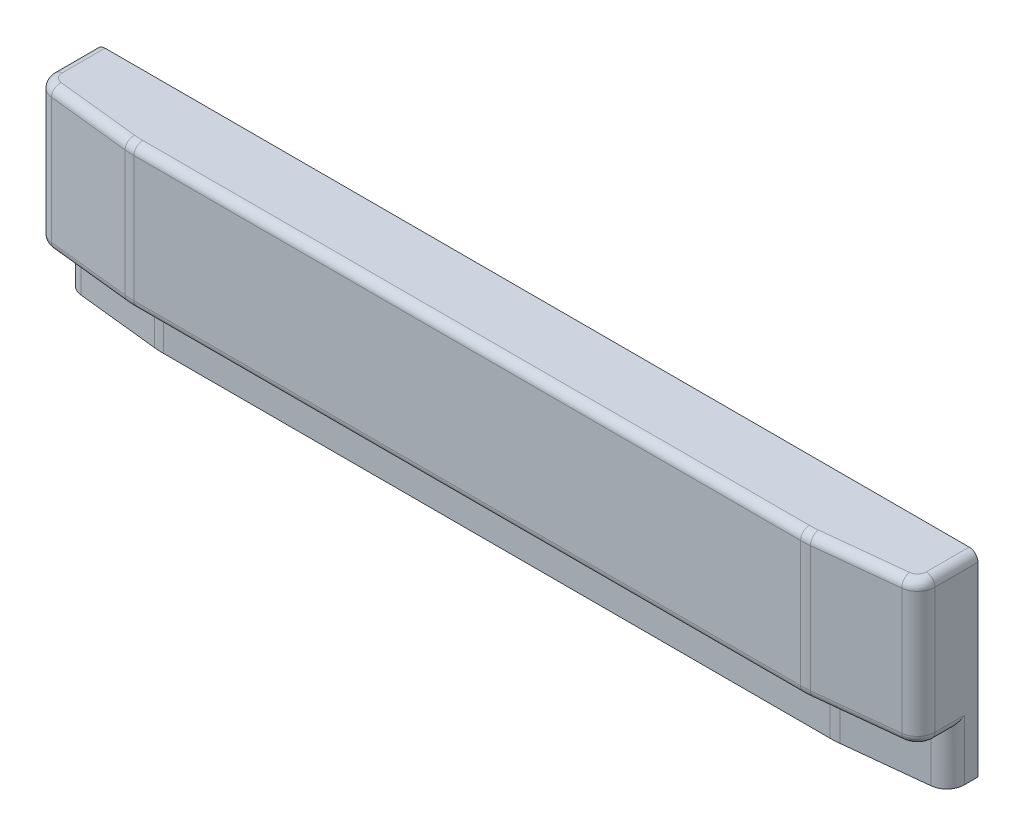
SolidWorks part; units mm, degrees
other "Camera1"
ref_plane "Front Plane" through (0, 0, 0) normal (0, 0, 1) x (1, 0, 0)
ref_plane "Top Plane" through (0, 0, 0) normal (0, 1, 0) x (1, 0, 0)
ref_plane "Right Plane" through (0, 0, 0) normal (1, 0, 0) x (0, 0, -1)
sketch "Sketch7" plane through (0, 0, 0) normal (0, 1, 0) x (1, 0, 0)
  line L0 (0, 0) -> (762, 0)
  line L1 (762, 0) -> (762, -50.8)
  line L2 (762, -50.8) -> (673.1, -60.325)
  line L3 (673.1, -60.325) -> (88.9, -60.325)
  line L4 (88.9, -60.325) -> (0, -50.8)
  line L5 (0, -50.8) -> (0, 0)
  dimension "D1" = 762
  dimension "D2" = 50.8
  dimension "D3" = 88.9
  dimension "D4" = 88.9
  dimension "D5" = 60.325
extrude "Boss-Extrude1" add sketch "Sketch7" along normal blind 168.275
ref_plane "Wall Plane" through (0, 0, 0) normal (0, 0, 1) x (1, 0, 0)
ref_plane "Floor Plane" through (0, 0, 0) normal (0, 1, 0) x (1, 0, 0)
sketch "Sketch10" plane through (0, 0, 0) normal (0, -1, 0) x (1, 0, 0)
  line L0 (0, 50.8) -> (0, 25.4)
  line L1 (0, 0) -> (0, 50.8) construction
  line L2 (0, 25.4) -> (88.9, 34.925)
  line L3 (88.9, 34.925) -> (673.1, 34.925)
  line L4 (673.1, 34.925) -> (762, 25.4)
  line L5 (762, 50.8) -> (762, 0) construction
  line L6 (762, 25.4) -> (762, 50.8)
  line L7 (762, 50.8) -> (673.1, 60.325)
  line L8 (673.1, 60.325) -> (88.9, 60.325)
  line L9 (88.9, 60.325) -> (0, 50.8)
  dimension "D1" = 25.4
extrude "Cut-Extrude1" cut sketch "Sketch10" against normal blind 44.45
fillet "Fillet1" radius 15.24 4 edges at (762, 22.225, 25.4) (762, 106.3625, 50.8) (0, 22.225, 25.4) (0, 106.3625, 50.8)
fillet "Fillet2" radius 76.2 4 edges at (673.1, 22.225, 34.925) (673.1, 106.3625, 60.325) (88.9, 22.225, 34.925) (88.9, 106.3625, 60.325)
fillet "Fillet3" radius 7.62 9 edges at (0, 168.275, 18.5528) (3.9042, 168.275, 47.2918) (49.2346, 168.275, 56.0751) (88.9058, 168.275, 60.2165) (762, 168.275, 18.5528) (758.0958, 168.275, 47.2918) (712.7654, 168.275, 56.0751) (673.0942, 168.275, 60.2165) (381, 168.275, 60.325)
fillet "Fillet4" radius 7.62 9 edges at (762, 44.45, 24.4056) (758.0958, 44.45, 47.2918) (712.7654, 44.45, 56.0751) (673.0942, 44.45, 60.2165) (0, 44.45, 24.4056) (3.9042, 44.45, 47.2918) (49.2346, 44.45, 56.0751) (88.9058, 44.45, 60.2165) (381, 44.45, 60.325)
